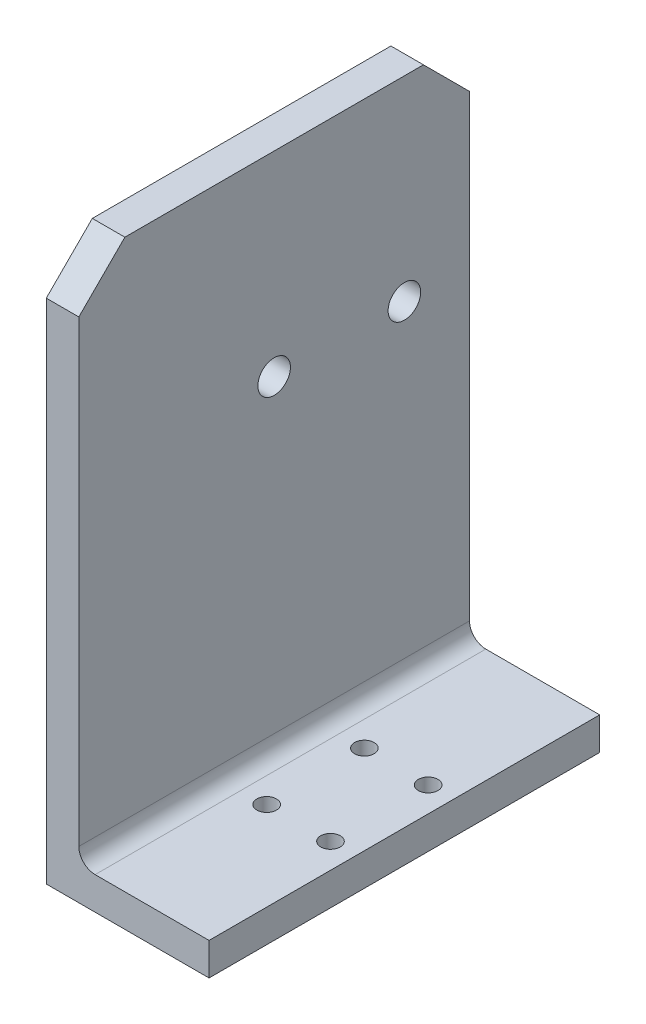
SolidWorks part; units mm, degrees
ref_plane "Front Plane" through (0, 0, 0) normal (0, 0, 1) x (1, 0, 0)
ref_plane "Top Plane" through (0, 0, 0) normal (0, 1, 0) x (1, 0, 0)
ref_plane "Right Plane" through (0, 0, 0) normal (1, 0, 0) x (0, 0, -1)
sketch "Sketch1" plane through (0, 0, 0) normal (0, 1, 0) x (1, 0, 0)
  line L0 (-28.6508, 0) -> (24.4776, 0) construction
  line L1 (-12.5, 30) -> (12.5, 30)
  line L2 (-12.5, 30) -> (-12.5, -30)
  line L3 (-12.5, -30) -> (12.5, -30)
  line L4 (12.5, 30) -> (12.5, -30)
  line L5 (-12.5, 30) -> (12.5, -30) construction
  line L6 (-12.5, -30) -> (12.5, 30) construction
  line L7 (-1.15, 9.9015) -> (-1.15, -43.5479) construction
  point P0 (0, 0)
  point P10 (-1.15, 7.5)
  point P11 (-1.15, -7.5)
  dimension "D1" = 25
  dimension "D2" = 60
  dimension "D3" = 11.35
  dimension "D4" = 15
extrude "Boss-Extrude1" add sketch "Sketch1" along normal blind 5
sketch "Sketch8" plane through (0, 5, 0) normal (0, 1, 0) x (1, 0, 0)
  line L0 (-12.5, -30) -> (12.5, -30) construction
  line L1 (-12.5, 30) -> (-7.5, 30)
  line L2 (-12.5, 30) -> (-12.5, -30)
  line L3 (-12.5, -30) -> (-7.5, -30)
  line L4 (-7.5, 30) -> (-7.5, -30)
  dimension "D1" = 5
extrude "Boss-Extrude2" add sketch "Sketch8" along normal blind 80
sketch "Sketch9" plane through (-7.5, 0, 0) normal (1, 0, 0) x (0, 0, -1)
  line L1 (-30, 5) -> (30, 5) construction
  circle A0 centre (0, 55) radius 2.5
  dimension "D1" = 5
  dimension "D2" = 50
extrude "Cut-Extrude1" cut sketch "Sketch9" against normal up to surface (5 mm away) up to face at (-12.5, 42.5, 0)
sketch "Sketch10" plane through (-7.5, 0, 0) normal (1, 0, 0) x (0, 0, -1)
  line L0 (-30, 77.9289) -> (-22.9289, 85)
  line L1 (22.9289, 85) -> (30, 77.9289)
  line L2 (-30, 85) -> (-22.9289, 85)
  line L7 (-30, 85) -> (-30, 77.9289)
  line L8 (30, 85) -> (30, 77.9289)
  line L9 (30, 85) -> (30, 5) construction
  line L10 (-30, 85) -> (-30, 5) construction
  line L11 (22.9289, 85) -> (30, 85)
  dimension "D1" = 45
  dimension "D2" = 45
  dimension "D3" = 5
  dimension "D4" = 5
extrude "Cut-Extrude2" cut sketch "Sketch10" against normal up to next
fillet "Fillet1" radius 2.5 1 edges at (-7.5, 5, 0)
ref_plane "Plane1" through (3.75, 0, 0) normal (1, 0, 0) x (0, 0, -1)
hole_wizard "Ø3.0mm Dowel Hole2" positions "Sketch13" profile "Sketch14" hole size "Ø3.0" standard "ANSI Metric" end condition through all
sketch "Sketch13" plane through (0, 5, 0) normal (0, 1, 0) x (1, 0, 0)
  point P0 (-1.15, -7.5)
  point P3 (-1.15, 7.5)
sketch "Sketch14" plane through (-1.15, 5, 7.5) normal (1, 0, 0) x (0, 0, 1)
  line L0 (0, 0) -> (0, 5)
  line L1 (0, 5) -> (1.5, 5)
  line L2 (1.5, 5) -> (1.5, 0)
  line L5 (1.5, 0) -> (0, 0)
  line L11 (0, -6.35) -> (0, 107.95) construction
  dimension "Thru Hole Dia." = 3
  dimension "Thru Hole Depth" = 5
mirror "Mirror1" about plane through (3.75, 0, 0) normal (1, 0, 0) of "Ø3.0mm Dowel Hole2"
sketch "Sketch15" plane through (-7.5, 0, 0) normal (1, 0, 0) x (0, 0, -1)
  line L0 (0, -11.7239) -> (0, 117.5809) construction
  line L1 (-90.5824, 55) -> (78.2528, 55) construction
  line L2 (-30, 0) -> (30, 0) construction
  line L3 (-30, 0) -> (30, 0) construction
  circle A1 centre (20, 55) radius 2.5
  point P10 (0, 0)
  point P14 (0, 0)
  dimension "D1" = 55
extrude "Cut-Extrude3" cut sketch "Sketch15" against normal through all
